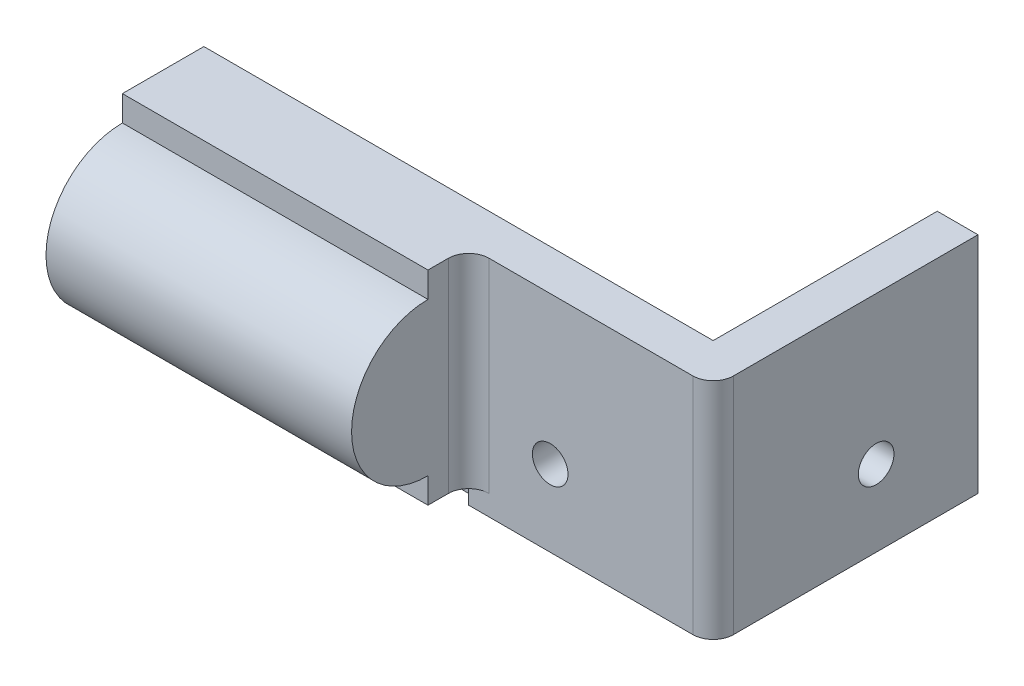
SolidWorks part; units mm, degrees
ref_plane "Front Plane" through (0, 0, 0) normal (0, 0, 1) x (1, 0, 0)
ref_plane "Top Plane" through (0, 0, 0) normal (0, 1, 0) x (1, 0, 0)
ref_plane "Right Plane" through (0, 0, 0) normal (1, 0, 0) x (0, 0, -1)
sketch "Sketch1" plane through (0, 0, 0) normal (0, 0, 1) x (1, 0, 0)
  line L1 (0, 0) -> (50, 0)
  line L2 (0, 0) -> (0, 30)
  line L3 (0, 30) -> (50, 30)
  line L4 (50, 0) -> (50, 30)
  dimension "D1" = 30
  dimension "D2" = 50
extrude "Boss-Extrude1" add sketch "Sketch1" along normal blind 3
sketch "Sketch2" plane through (0, 0, 3) normal (0, 0, 1) x (1, 0, 0)
  line L0 (0, 0) -> (50, 0) construction
  line L1 (50, 0) -> (50, 30) construction
  circle A0 centre (38, 7.5) radius 1.75
  dimension "D1" = 3.5
  dimension "D2" = 7.5
  dimension "D3" = 12
extrude "Cut-Extrude1" cut sketch "Sketch2" against normal through all
sketch "Sketch3" plane through (0, 0, 3) normal (0, 0, 1) x (1, 0, 0)
  line L0 (0, 30) -> (0, 0) construction
  line L1 (0, 2) -> (30, 2)
  line L2 (0, 2) -> (0, 22)
  line L3 (0, 22) -> (30, 22)
  line L4 (30, 2) -> (30, 22)
  line L5 (0, 0) -> (50, 0) construction
  dimension "D1" = 30
  dimension "D2" = 2
  dimension "D3" = 20
extrude "Boss-Extrude2" add sketch "Sketch3" along normal blind 5
sketch "Sketch4" plane through (0, 0, 0) normal (-1, 0, 0) x (0, 0, 1)
  line L0 (8, 22) -> (8, 2) construction
  line L1 (8, 22) -> (3, 22) construction
  line L2 (8, 4.5) -> (8, 19.5)
  arc A0 (8, 4.5) -> (8, 19.5) centre (8, 12) ccw
  dimension "D1" = 15
  dimension "D2" = 10
extrude "Boss-Extrude3" add sketch "Sketch4" against normal blind 30
sketch "Sketch5" plane through (0, 0, 0) normal (-1, 0, 0) x (0, 0, 1)
  circle A0 centre (8, 12) radius 4
  arc A1 (8, 4.5) -> (8, 19.5) centre (8, 12) ccw construction
  dimension "D1" = 8
extrude "Cut-Extrude2" cut sketch "Sketch5" against normal blind 20
sketch "Sketch6" plane through (0, 0, 3) normal (0, 0, 1) x (1, 0, 0)
  line L0 (50, 0) -> (50, 30) construction
  line L1 (0, 22) -> (50, 22)
  line L2 (0, 22) -> (0, 30)
  line L3 (0, 30) -> (50, 30)
  line L4 (50, 22) -> (50, 30)
  line L7 (30, 22) -> (0, 22) construction
  line L8 (50, 30) -> (0, 30) construction
  line L9 (0, 30) -> (0, 22) construction
extrude "Cut-Extrude3" cut sketch "Sketch6" against normal blind 20
sketch "Sketch7" plane through (50, 0, 0) normal (1, 0, 0) x (0, 0, -1)
  line L0 (-3, 0) -> (-3, 22) construction
  line L1 (-3, 0) -> (0, 0)
  line L2 (-3, 0) -> (-3, 22)
  line L3 (-3, 22) -> (0, 22)
  line L4 (0, 0) -> (0, 22)
  line L5 (0, 22) -> (-3, 22) construction
  line L6 (0, 0) -> (0, 22) construction
  line L7 (-3, 0) -> (0, 0) construction
extrude "Boss-Extrude4" add sketch "Sketch7" along normal blind 3
sketch "Sketch8" plane through (0, 0, 0) normal (0, 0, -1) x (-1, 0, 0)
  line L0 (-53, 0) -> (-53, 22) construction
  line L1 (-53, 0) -> (-50, 0)
  line L2 (-53, 0) -> (-53, 22)
  line L3 (-53, 22) -> (-50, 22)
  line L4 (-50, 0) -> (-50, 22)
  line L5 (-53, 22) -> (0, 22) construction
  dimension "D1" = 3
extrude "Boss-Extrude5" add sketch "Sketch8" along normal blind 22
sketch "Sketch9" plane through (53, 0, 0) normal (1, 0, 0) x (0, 0, -1)
  line L0 (-3, 22) -> (-3, 0) construction
  line L1 (-3, 0) -> (22, 0) construction
  circle A0 centre (12, 7.5) radius 1.75
  dimension "D1" = 3.5
  dimension "D2" = 15
  dimension "D3" = 7.5
extrude "Cut-Extrude4" cut sketch "Sketch9" against normal through all
sketch "Sketch10" plane through (0, 0, 3) normal (0, 0, 1) x (1, 0, 0)
  line L0 (30, 22) -> (53, 22) construction
  line L1 (53, 22) -> (30, 22)
  line L2 (53, 22) -> (53, 0)
  line L3 (53, 0) -> (30, 0)
  line L4 (30, 22) -> (30, 0)
  line L5 (0, 0) -> (53, 0) construction
  line L6 (53, 22) -> (53, 0) construction
  line L7 (30, 2) -> (30, 22) construction
  circle A0 centre (38, 7.5) radius 1.75
  circle A1 centre (38, 7.5) radius 1.75 construction
extrude "Boss-Extrude6" add sketch "Sketch10" along normal blind 1
sketch "Sketch11" plane through (53, 0, 0) normal (1, 0, 0) x (0, 0, -1)
  line L0 (22, 22) -> (22, 0) construction
  line L1 (22, 0) -> (-4, 0)
  line L2 (22, 0) -> (22, 22)
  line L3 (22, 22) -> (-4, 22)
  line L4 (-4, 0) -> (-4, 22)
  line L5 (-4, 0) -> (22, 0) construction
  line L6 (-4, 0) -> (-4, 22) construction
  line L7 (22, 22) -> (-4, 22) construction
  circle A0 centre (12, 7.5) radius 1.75
  circle A1 centre (12, 7.5) radius 1.75 construction
extrude "Boss-Extrude7" add sketch "Sketch11" along normal blind 1
fillet "Fillet1" radius 2 2 edges at (30, 12, 4) (54, 11, 4)
